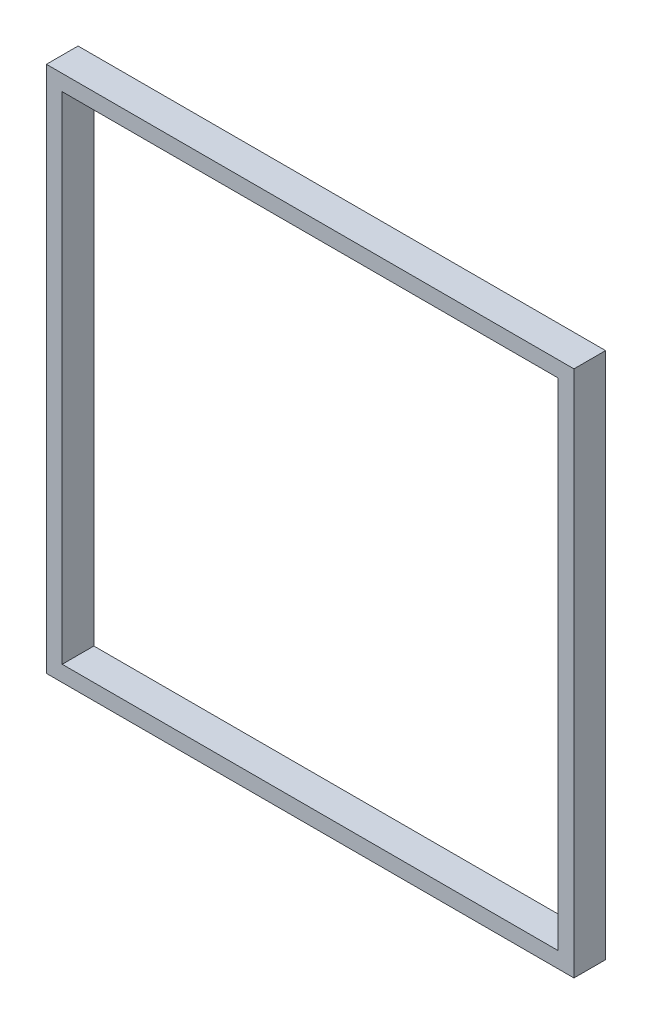
SolidWorks part; units mm, degrees
ref_plane "Front Plane" through (0, 0, 0) normal (0, 0, 1) x (1, 0, 0)
ref_plane "Top Plane" through (0, 0, 0) normal (0, 1, 0) x (1, 0, 0)
ref_plane "Right Plane" through (0, 0, 0) normal (1, 0, 0) x (0, 0, -1)
sketch "Sketch1" plane through (0, 0, 0) normal (0, 0, 1) x (1, 0, 0)
  line L0 (1.5, 48.5) -> (48.5, 48.5)
  line L1 (0, 0) -> (50, 0)
  line L2 (0, 0) -> (0, 50)
  line L3 (0, 50) -> (50, 50)
  line L4 (50, 0) -> (50, 50)
  line L5 (48.5, 1.5) -> (48.5, 48.5)
  line L6 (1.5, 1.5) -> (48.5, 1.5)
  line L7 (1.5, 1.5) -> (1.5, 48.5)
  dimension "D1" = 50
  dimension "D2" = 1.5
extrude "Boss-Extrude1" add sketch "Sketch1" along normal blind 3
